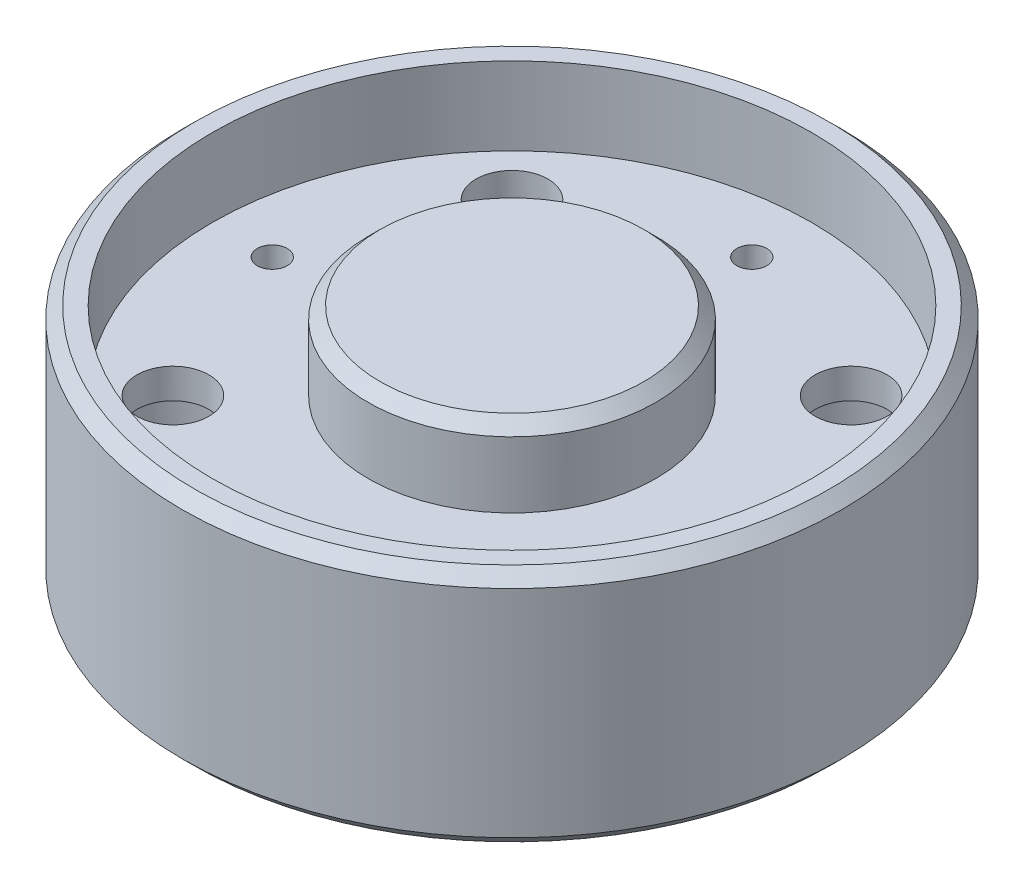
SolidWorks part; units mm, degrees
material "1060 Alloy"
ref_plane "Front Plane" through (0, 0, 0) normal (0, 0, 1) x (1, 0, 0)
ref_plane "Top Plane" through (0, 0, 0) normal (0, 1, 0) x (1, 0, 0)
ref_plane "Right Plane" through (0, 0, 0) normal (1, 0, 0) x (0, 0, -1)
sketch "Sketch1" plane through (0, 0, 0) normal (0, 0, 1) x (1, 0, 0)
  line L0 (0, -626.6874) -> (0, 30707.6802) construction
  line L1 (-626.6874, 0) -> (30707.6802, 0) construction
  line L3 (27.5, 0) -> (27.5, 20)
  line L4 (27.5, 20) -> (25, 20)
  line L5 (25, 20) -> (25, 13.5)
  line L6 (25, 13.5) -> (12, 13.5)
  line L7 (12, 13.5) -> (12, 20)
  line L8 (12, 20) -> (0, 20)
  line L10 (27.5, 0) -> (22.4, 0)
  line L11 (22.4, 0) -> (22.4, 5.5)
  line L12 (22.4, 5.5) -> (0, 5.5)
  line L13 (0, 20) -> (0, 5.5)
  point P4 (22.4, 2.75)
  dimension "D1" = 55
  dimension "D2" = 50
  dimension "D3" = 6.5
  dimension "D4" = 24
  dimension "D5" = 20
  dimension "D6" = 5.5
  dimension "D7" = 44.8
revolve "Revolve1" add sketch "Sketch1" angle 360 about L0
sketch "Sketch2" plane through (0, 0, 0) normal (0, 1, 0) x (1, 0, 0)
  line L0 (0, -1000) -> (0, 49000) construction
  line L1 (-14.1421, -14.1421) -> (14.1421, -14.1421) construction
  line L2 (-14.1421, -14.1421) -> (-14.1421, 14.1421) construction
  line L3 (-14.1421, 14.1421) -> (14.1421, 14.1421) construction
  line L4 (14.1421, -14.1421) -> (14.1421, 14.1421) construction
  line L5 (-14.1421, -14.1421) -> (14.1421, 14.1421) construction
  line L6 (-14.1421, 14.1421) -> (14.1421, -14.1421) construction
  line L7 (-1000, 0) -> (49000, 0) construction
  circle A0 centre (-14.1421, 14.1421) radius 3
  circle A1 centre (14.1421, 14.1421) radius 3
  circle A2 centre (14.1421, -14.1421) radius 3
  circle A3 centre (-14.1421, -14.1421) radius 3
  point P0 (0, 0)
  dimension "D2" = 6
  dimension "D1" = 40
extrude "Cut-Extrude2" cut sketch "Sketch2" against normal through all and the other way through all
sketch "Sketch3" plane through (0, 0, 0) normal (0, -1, 0) x (1, 0, 0)
  line L0 (0, -1000) -> (0, 49000) construction
  line L1 (-1000, 0) -> (49000, 0) construction
  circle A0 centre (-14.1421, 14.1421) radius 5.5
  circle A1 centre (14.1421, 14.1421) radius 5.5
  circle A2 centre (14.1421, -14.1421) radius 5.5
  circle A3 centre (-14.1421, -14.1421) radius 5.5
  dimension "D1" = 11
extrude "Cut-Extrude3" cut sketch "Sketch3" against normal blind 11
sketch "Sketch4" plane through (0, 5.5, 0) normal (0, -1, 0) x (1, 0, 0)
  line L0 (0, -1000) -> (0, 49000) construction
  line L1 (-1000, 0) -> (49000, 0) construction
  line L3 (0, 20) -> (-20, 0) construction
  line L4 (0, 20) -> (20, 0) construction
  line L5 (20, 0) -> (0, -20) construction
  line L6 (-20, 0) -> (0, -20) construction
  line L7 (0, 20) -> (0, -20) construction
  line L8 (20, 0) -> (-20, 0) construction
  circle A0 centre (0, 20) radius 1.25
  circle A1 centre (-20, 0) radius 1.25
  circle A2 centre (0, -20) radius 1.25
  circle A3 centre (20, 0) radius 1.25
  point P4 (0, 0)
  dimension "D2" = 2.5
  dimension "D1" = 40
extrude "Cut-Extrude4" cut sketch "Sketch4" against normal up to next
cosmetic thread "Cosmetic Thread1" parameters "D1"=6, "D2"=3
cosmetic thread "Cosmetic Thread2" parameters "D1"=6, "D2"=3
cosmetic thread "Cosmetic Thread3" parameters "D1"=6, "D2"=3
cosmetic thread "Cosmetic Thread4" parameters "D1"=6, "D2"=3
chamfer "Chamfer1" distance 1 angle 45 3 edges at (12, 20, 0) (27.5, 20, 0) (27.5, 0, 0)
